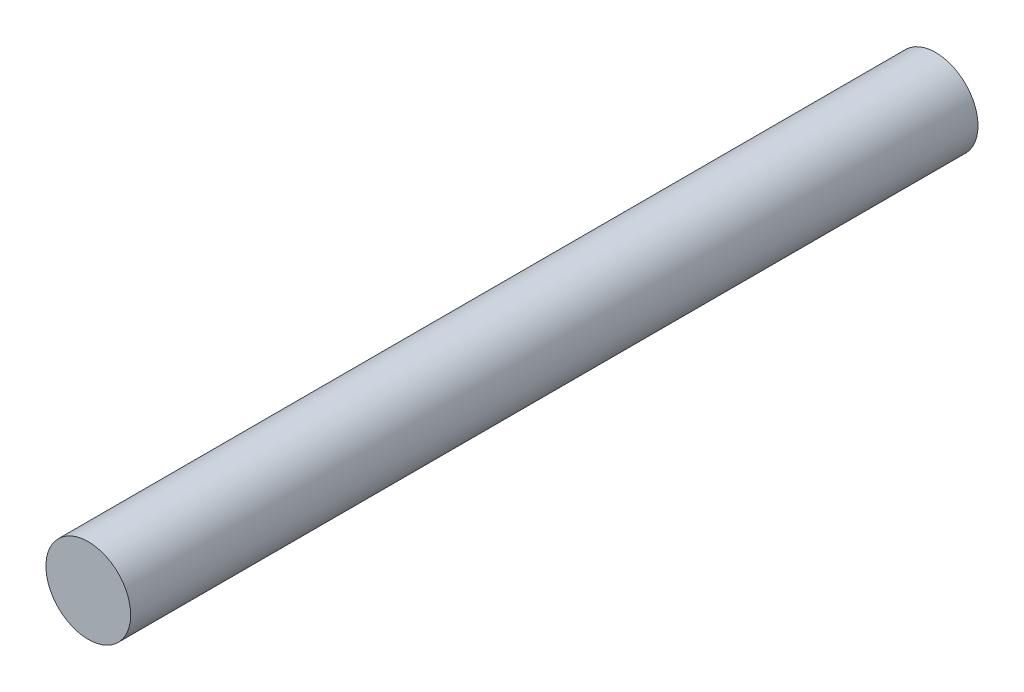
SolidWorks part; units mm, degrees
material "环氧板3240"
ref_plane "前视基准面" through (0, 0, 0) normal (0, 0, 1) x (1, 0, 0)
ref_plane "上视基准面" through (0, 0, 0) normal (0, 1, 0) x (1, 0, 0)
ref_plane "右视基准面" through (0, 0, 0) normal (1, 0, 0) x (0, 0, -1)
other "Configuration Table"
sketch "草图1" plane through (0, 0, 0) normal (0, 0, 1) x (1, 0, 0)
  circle A0 centre (71.8331, 2.8195) radius 4
  dimension "D1" = 8
extrude "凸台-拉伸1" add sketch "草图1" along normal blind 80
